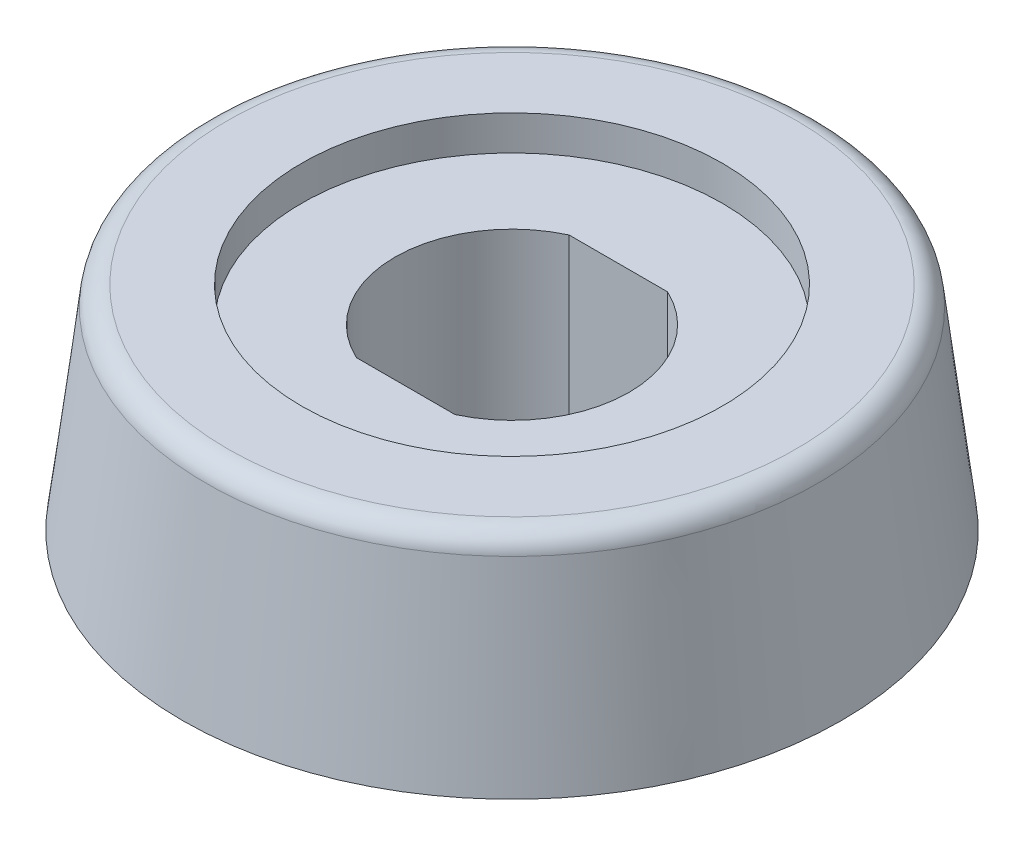
SolidWorks part; units mm, degrees
ref_plane "Alzado" through (0, 0, 0) normal (0, 0, 1) x (1, 0, 0)
ref_plane "Planta" through (0, 0, 0) normal (0, 1, 0) x (1, 0, 0)
ref_plane "Vista lateral" through (0, 0, 0) normal (1, 0, 0) x (0, 0, -1)
ref_plane "Plano1" through (0, 0, 0) normal (0, -1, 0) x (1, 0, 0)
sketch "Croquis1" plane through (0, 0, 0) normal (0, -1, 0) x (1, 0, 0)
  line L0 (-9.325, -7.6) -> (9.325, -7.6)
  line L1 (9.325, 7.6) -> (-9.325, 7.6)
  arc A0 (-9.325, 7.6) -> (-9.325, -7.6) centre (-9.325, 0) ccw
  arc A1 (9.325, -7.6) -> (9.325, 7.6) centre (9.325, 0) ccw
extrude "Saliente-Extruir1" add sketch "Croquis1" against normal blind 4.9 draft 7
sketch "Croquis2" plane through (0, 0, 0) normal (0, -1, 0) x (1, 0, 0)
  circle A0 centre (9.325, 0) radius 5.8
extrude "Saliente-Extruir2" add sketch "Croquis2" along normal blind 0.3
sketch "Croquis3" plane through (0, 4.9, 0) normal (0, 1, 0) x (-1, 0, 0)
  line L0 (-10.4597, -2.45) -> (-8.1903, -2.45)
  line L1 (-8.1903, 2.45) -> (-10.4597, 2.45)
  arc A0 (-8.1903, -2.45) -> (-8.1903, 2.45) centre (-9.325, 0) ccw
  arc A1 (-10.4597, 2.45) -> (-10.4597, -2.45) centre (-9.325, 0) ccw
extrude "Cortar-Extruir1" cut sketch "Croquis3" against normal through all
sketch "Croquis4" plane through (0, 0, 0) normal (0, -1, 0) x (1, 0, 0)
  circle A0 centre (-9.325, 0) radius 5.8
extrude "Saliente-Extruir3" add sketch "Croquis4" along normal blind 0.3
sketch "Croquis5" plane through (0, 4.9, 0) normal (0, 1, 0) x (-1, 0, 0)
  line L0 (10.4597, 2.45) -> (8.1903, 2.45)
  line L1 (8.1903, -2.45) -> (10.4597, -2.45)
  arc A0 (8.1903, 2.45) -> (8.1903, -2.45) centre (9.325, 0) ccw
  arc A1 (10.4597, -2.45) -> (10.4597, 2.45) centre (9.325, 0) ccw
extrude "Cortar-Extruir2" cut sketch "Croquis5" against normal through all
sketch "Croquis6" plane through (0, 0, 0) normal (0, -1, 0) x (1, 0, 0)
  line L0 (-2.15, 2.8) -> (-2.15, -2.8)
  line L1 (2.15, -2.8) -> (2.15, 2.8)
  arc A0 (-2.15, -2.8) -> (2.15, -2.8) centre (0, -2.8) ccw
  arc A1 (2.15, 2.8) -> (-2.15, 2.8) centre (0, 2.8) ccw
extrude "Cortar-Extruir3" cut sketch "Croquis6" against normal blind 3.75
ref_plane "Plano2" through (-9.325, 0, 0) normal (1, 0, 0) x (0, 0, -1)
sketch "Croquis7" plane through (-9.325, 0, 0) normal (1, 0, 0) x (0, 0, -1)
  line L0 (4.85, 5) -> (0, 5)
  line L1 (0, 5) -> (0, 4.1)
  line L2 (0, 4.1) -> (4.85, 4.1)
  line L3 (4.85, 4.1) -> (4.85, 5)
  line L4 (0, 5) -> (0, 4.1) construction
revolve "Cortar-Revolución1" cut sketch "Croquis7" angle 360 about L4
ref_plane "Plano3" through (9.325, 0, 0) normal (1, 0, 0) x (0, 0, -1)
sketch "Croquis8" plane through (9.325, 0, 0) normal (1, 0, 0) x (0, 0, -1)
  line L0 (4.85, 5) -> (0, 5)
  line L1 (0, 5) -> (0, 4.1)
  line L2 (0, 4.1) -> (4.85, 4.1)
  line L3 (4.85, 4.1) -> (4.85, 5)
  line L4 (0, 5) -> (0, 4.1) construction
revolve "Cortar-Revolución2" cut sketch "Croquis8" angle 360 about L4
sketch "Croquis9" plane through (-9.325, 0, 0) normal (1, 0, 0) x (0, 0, -1)
  line L0 (3.415, 0) -> (0, 0)
  line L1 (0, 0) -> (0, -0.3)
  line L2 (0, -0.3) -> (3.415, -0.3)
  line L3 (3.415, -0.3) -> (3.415, 0)
  line L4 (0, 0) -> (0, -0.3) construction
revolve "Cortar-Revolución3" cut sketch "Croquis9" angle 360 about L4
sketch "Croquis10" plane through (9.325, 0, 0) normal (1, 0, 0) x (0, 0, -1)
  line L0 (3.415, 0) -> (0, 0)
  line L1 (0, 0) -> (0, -0.3)
  line L2 (0, -0.3) -> (3.415, -0.3)
  line L3 (3.415, -0.3) -> (3.415, 0)
  line L4 (0, 0) -> (0, -0.3) construction
revolve "Cortar-Revolución4" cut sketch "Croquis10" angle 360 about L4
sketch "Croquis11" plane through (0, 0, 0) normal (0, 1, 0) x (1, 0, 0)
  circle A0 centre (-9.325, 0) radius 6.99
extrude "Cortar-Extruir8" cut sketch "Croquis11" against normal through all both and the other way through all flip side to cut contours A0
sketch "Croquis20" plane through (0, 0, 0) normal (0, -1, 0) x (1, 0, 0)
  circle A0 centre (-9.325, 0) radius 7.6
  circle A1 centre (-9.325, 0) radius 5.8
extrude "Saliente-Extruir11" add sketch "Croquis20" against normal blind 4.9 draft 7
fillet "Redondeo6" radius 0.5 1 edges at (-9.325, 4.9, -6.9984)
